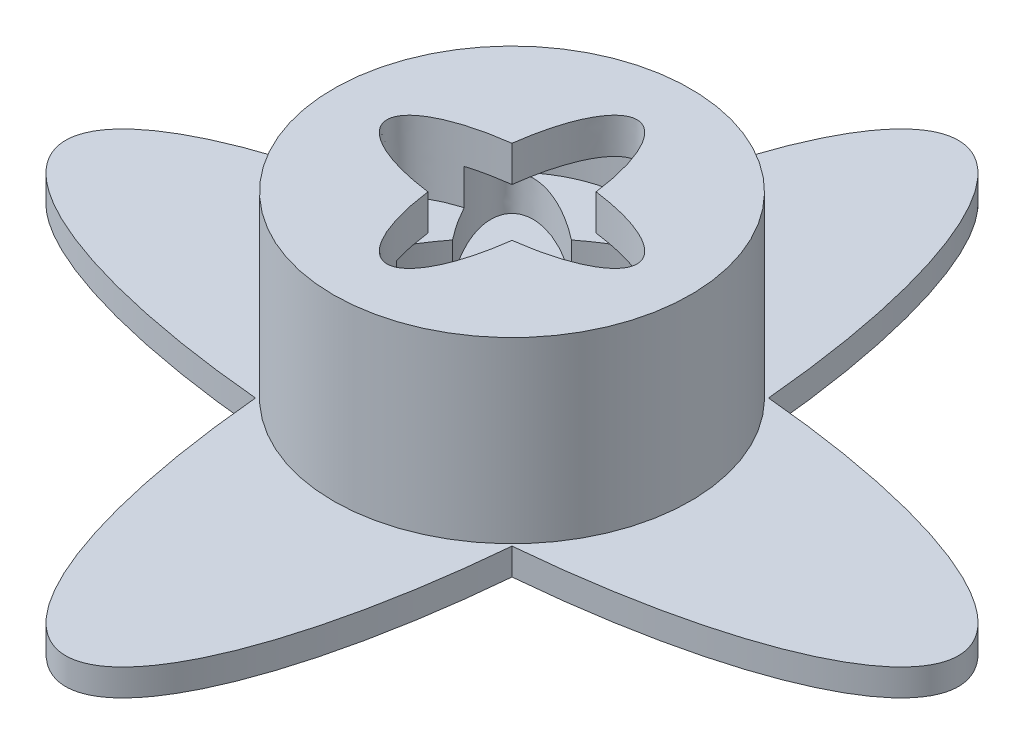
SolidWorks part; units mm, degrees
ref_plane "Front Plane" through (0, 0, 0) normal (0, 0, 1) x (1, 0, 0)
ref_plane "Top Plane" through (0, 0, 0) normal (0, 1, 0) x (1, 0, 0)
ref_plane "Right Plane" through (0, 0, 0) normal (1, 0, 0) x (0, 0, -1)
sketch "Sketch1" plane through (0, 0, 0) normal (0, 1, 0) x (1, 0, 0)
  ellipse E0 centre (0, 0) end of major axis (0, -25) minor radius 7.5 (7.1837, 7.1837) -> (-7.1837, 7.1837) ccw
  ellipse E1 centre (0, 0) end of major axis (-25, 0) minor radius 7.5 (-7.1837, 7.1837) -> (-7.1837, -7.1837) ccw
  ellipse E2 centre (0, 0) end of major axis (0, -25) minor radius 7.5 (-7.1837, -7.1837) -> (7.1837, -7.1837) ccw
  ellipse E3 centre (0, 0) end of major axis (-25, 0) minor radius 7.5 (7.1837, -7.1837) -> (7.1837, 7.1837) ccw
  point P14 (0, 0)
extrude "Boss-Extrude1" add sketch "Sketch1" along normal blind 1.5
sketch "Sketch2" plane through (0, 1.5, 0) normal (0, 1, 0) x (1, 0, 0)
  circle A0 centre (0, 0) radius 10
  point P22 (0, 0)
extrude "Boss-Extrude2" add sketch "Sketch2" along normal blind 10
sketch "Sketch3" plane through (0, 0, 0) normal (0, -1, 0) x (1, 0, 0)
  circle A0 centre (0, 0) radius 2.5
extrude "Cut-Extrude1" cut sketch "Sketch3" against normal blind 2.5
sketch "Sketch4" plane through (0, 11.5, 0) normal (0, 1, 0) x (1, 0, 0)
  ellipse E0 centre (0, 0) end of major axis (0, -7) minor radius 2.5 (-2.3544, -2.3544) -> (2.3544, -2.3544) ccw
  ellipse E1 centre (0, 0) end of major axis (-7, 0) minor radius 2.5 (2.3544, -2.3544) -> (2.3544, 2.3544) ccw
  ellipse E2 centre (0, 0) end of major axis (-7, 0) minor radius 2.5 (-2.3544, 2.3544) -> (-2.3544, -2.3544) ccw
  ellipse E3 centre (0, 0) end of major axis (0, -7) minor radius 2.5 (2.3544, 2.3544) -> (-2.3544, 2.3544) ccw
  point P14 (0, 0)
  point P16 (0, 0)
extrude "Cut-Extrude2" cut sketch "Sketch4" against normal blind 4
sketch "Sketch5" plane through (0, 7.5, 0) normal (0, 1, 0) x (1, 0, 0)
  arc A4 (7, 0) -> (4.9497, 4.9497) centre (0, 0) ccw
  arc A5 (0, 7) -> (-4.9497, 4.9497) centre (0, 0) ccw
  arc A6 (-7, 0) -> (-4.9497, -4.9497) centre (0, 0) ccw
  arc A7 (0, -7) -> (4.9497, -4.9497) centre (0, 0) ccw
  ellipse E1 centre (0, 0) end of major axis (-7, 0) minor radius 2.5 (4.571, -1.8934) -> (7, 0) ccw
  ellipse E2 centre (0, 0) end of major axis (-4.9497, -4.9497) minor radius 2.5 (4.9497, 4.9497) -> (1.8934, 4.571) ccw
  ellipse E3 centre (0, 0) end of major axis (-4.9497, 4.9497) minor radius 2.5 (-4.9497, 4.9497) -> (-4.571, 1.8934) ccw
  ellipse E4 centre (0, 0) end of major axis (0, -7) minor radius 2.5 (1.8934, 4.571) -> (0, 7) ccw
  ellipse E6 centre (0, 0) end of major axis (0, -7) minor radius 2.5 (-1.8934, -4.571) -> (0, -7) ccw
  ellipse E7 centre (0, 0) end of major axis (-4.9497, -4.9497) minor radius 2.5 (-4.9497, -4.9497) -> (-1.8934, -4.571) ccw
  ellipse E8 centre (0, 0) end of major axis (-7, 0) minor radius 2.5 (-4.571, 1.8934) -> (-7, 0) ccw
  ellipse E9 centre (0, 0) end of major axis (-4.9497, 4.9497) minor radius 2.5 (4.9497, -4.9497) -> (4.571, -1.8934) ccw
  point P15 (0, 0)
  point P16 (0, 0)
  point P26 (0, 0)
  point P27 (0, 0)
extrude "Cut-Extrude3" cut sketch "Sketch5" along normal blind 2
sketch "Sketch6" plane through (0, 7.5, 0) normal (0, 1, 0) x (1, 0, 0)
  ellipse E0 centre (0, 0) end of major axis (-4.9497, -4.9497) minor radius 2.5 (-3.3296, 0) -> (0, -3.3296) ccw
  ellipse E2 centre (0, 0) end of major axis (-4.9497, 4.9497) minor radius 2.5 (0, 3.3296) -> (-3.3296, 0) ccw
  ellipse E3 centre (0, 0) end of major axis (-4.9497, -4.9497) minor radius 2.5 (3.3296, 0) -> (0, 3.3296) ccw
  ellipse E4 centre (0, 0) end of major axis (-4.9497, 4.9497) minor radius 2.5 (0, -3.3296) -> (3.3296, 0) ccw
  point P14 (0, 0)
  point P22 (0, 0)
  point P26 (0, 0)
  point P33 (0, 0)
extrude "Cut-Extrude4" cut sketch "Sketch6" against normal blind 2
